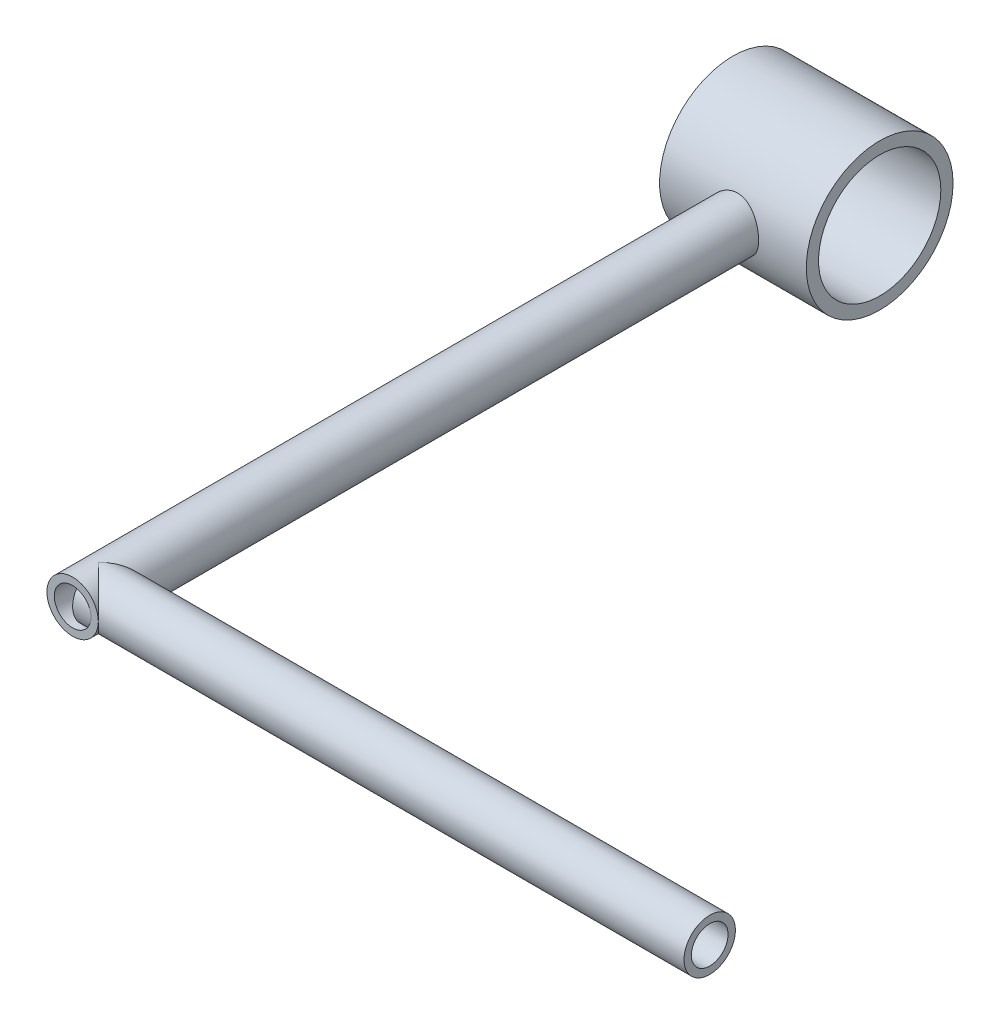
SolidWorks part; units mm, degrees
ref_plane "Спереди" through (0, 0, 0) normal (0, 0, 1) x (1, 0, 0)
ref_plane "Сверху" through (0, 0, 0) normal (0, 1, 0) x (1, 0, 0)
ref_plane "Справа" through (0, 0, 0) normal (1, 0, 0) x (0, 0, -1)
sketch "Эскиз1" plane through (0, 0, 0) normal (0, 0, 1) x (1, 0, 0)
  circle A0 centre (0, 0) radius 10.5
  dimension "D1" = 21
extrude "Бобышка-Вытянуть1" add sketch "Эскиз1" along normal blind 300
sketch "Эскиз2" plane through (0, 0, 0) normal (0, 0, -1) x (-1, 0, 0)
  circle A0 centre (0, 0) radius 7.5
  dimension "D1" = 15
extrude "Вырез-Вытянуть1" cut sketch "Эскиз2" against normal through all
sketch "Эскиз4" plane through (0, 0, 0) normal (1, 0, 0) x (0, 0, -1)
  circle A0 centre (0, 0) radius 30
  dimension "D1" = 60
extrude "Бобышка-Вытянуть2" add sketch "Эскиз4" along normal mid plane 60
sketch "Эскиз5" plane through (30, 0, 0) normal (1, 0, 0) x (0, 0, -1)
  circle A0 centre (0, 0) radius 25
  dimension "D1" = 50
extrude "Вырез-Вытянуть2" cut sketch "Эскиз5" against normal through all
sketch "Эскиз7" plane through (0, 0, 0) normal (1, 0, 0) x (0, 0, -1)
  circle A0 centre (-289.5, 0) radius 10.5
  circle A1 centre (-289.5, 0) radius 7.5
  dimension "D1" = 21
  dimension "D3" = 15
  dimension "D2" = 10.5
extrude "Бобышка-Вытянуть4" add sketch "Эскиз7" along normal blind 250
